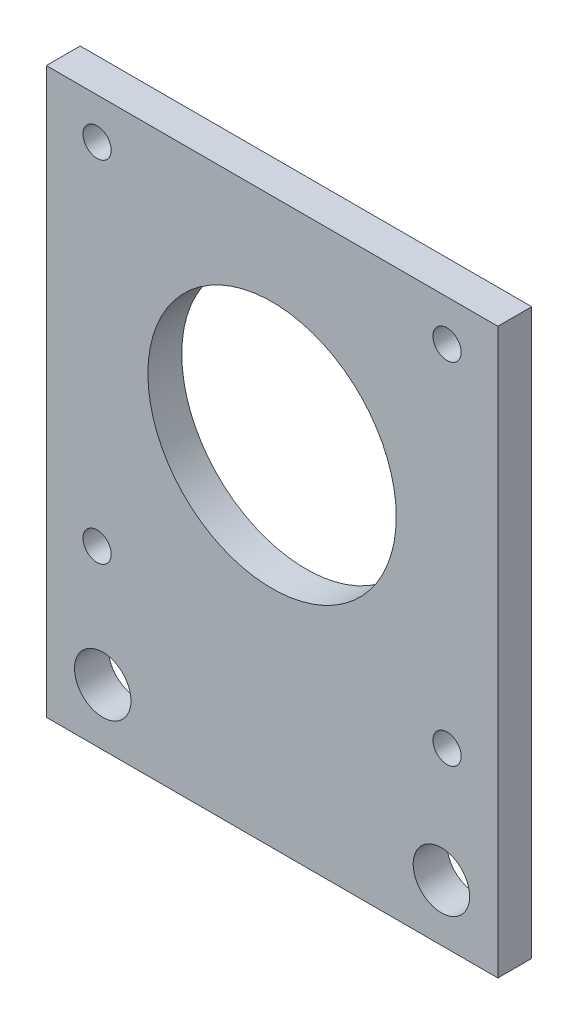
SolidWorks part; units mm, degrees
ref_plane "Front Plane" through (0, 0, 0) normal (0, 0, 1) x (1, 0, 0)
ref_plane "Top Plane" through (0, 0, 0) normal (0, 1, 0) x (1, 0, 0)
ref_plane "Right Plane" through (0, 0, 0) normal (1, 0, 0) x (0, 0, -1)
sketch "Sketch1" plane through (0, 0, 0) normal (0, 0, 1) x (1, 0, 0)
  line L0 (0, 25) -> (0, -25) construction
  line L1 (-20, 25) -> (20, 25)
  line L2 (-20, 25) -> (-20, -25)
  line L3 (-20, -25) -> (20, -25)
  line L4 (20, 25) -> (20, -25)
  line L5 (-20, 25) -> (20, -25) construction
  line L6 (-20, -25) -> (20, 25) construction
  line L7 (-15.5, 21.376) -> (15.5, 21.376) construction
  line L8 (-15.5, 21.376) -> (-15.5, -9.624) construction
  line L9 (-15.5, -9.624) -> (15.5, -9.624) construction
  line L10 (15.5, 21.376) -> (15.5, -9.624) construction
  line L11 (-15.5, 21.376) -> (15.5, -9.624) construction
  line L12 (-15.5, -9.624) -> (15.5, 21.376) construction
  circle A0 centre (-15.5, 21.376) radius 1.25
  circle A1 centre (-15.5, -9.624) radius 1.25
  circle A2 centre (15.5, 21.376) radius 1.25
  circle A3 centre (15.5, -9.624) radius 1.25
  circle A4 centre (-15, -20) radius 2.5
  circle A5 centre (15, -20) radius 2.5
  circle A6 centre (0, 5.876) radius 11
  point P0 (0, 0)
  point P6 (0, 5.876)
  dimension "D3" = 2.5
  dimension "D6" = 5
  dimension "D9" = 22
  dimension "D1" = 50
  dimension "D2" = 40
  dimension "D4" = 31
  dimension "D5" = 31
  dimension "D7" = 5
  dimension "D8" = 5
extrude "Boss-Extrude1" add sketch "Sketch1" along normal blind 3
